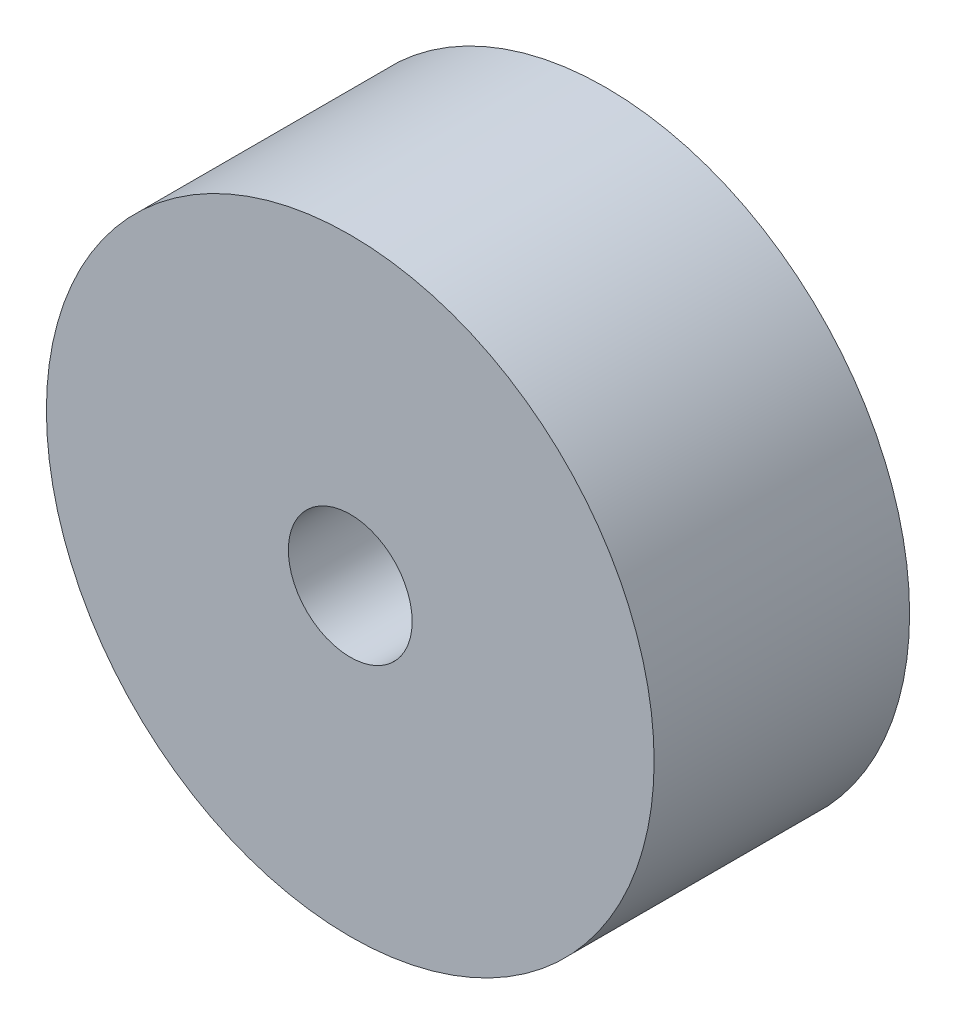
SolidWorks part; units mm, degrees
ref_plane "Front Plane" through (0, 0, 0) normal (0, 0, 1) x (1, 0, 0)
ref_plane "Top Plane" through (0, 0, 0) normal (0, 1, 0) x (1, 0, 0)
ref_plane "Right Plane" through (0, 0, 0) normal (1, 0, 0) x (0, 0, -1)
sketch "Sketch1" plane through (0, 0, 0) normal (0, 0, 1) x (1, 0, 0)
  circle A0 centre (0, 0) radius 12.025
extrude "Boss-Extrude1" add sketch "Sketch1" along normal blind 10.11
sketch "Sketch2" plane through (0, 0, 10.11) normal (0, 0, 1) x (1, 0, 0)
  circle A0 centre (0, 0) radius 2.45
extrude "Cut-Extrude1" cut sketch "Sketch2" against normal blind 10.11
